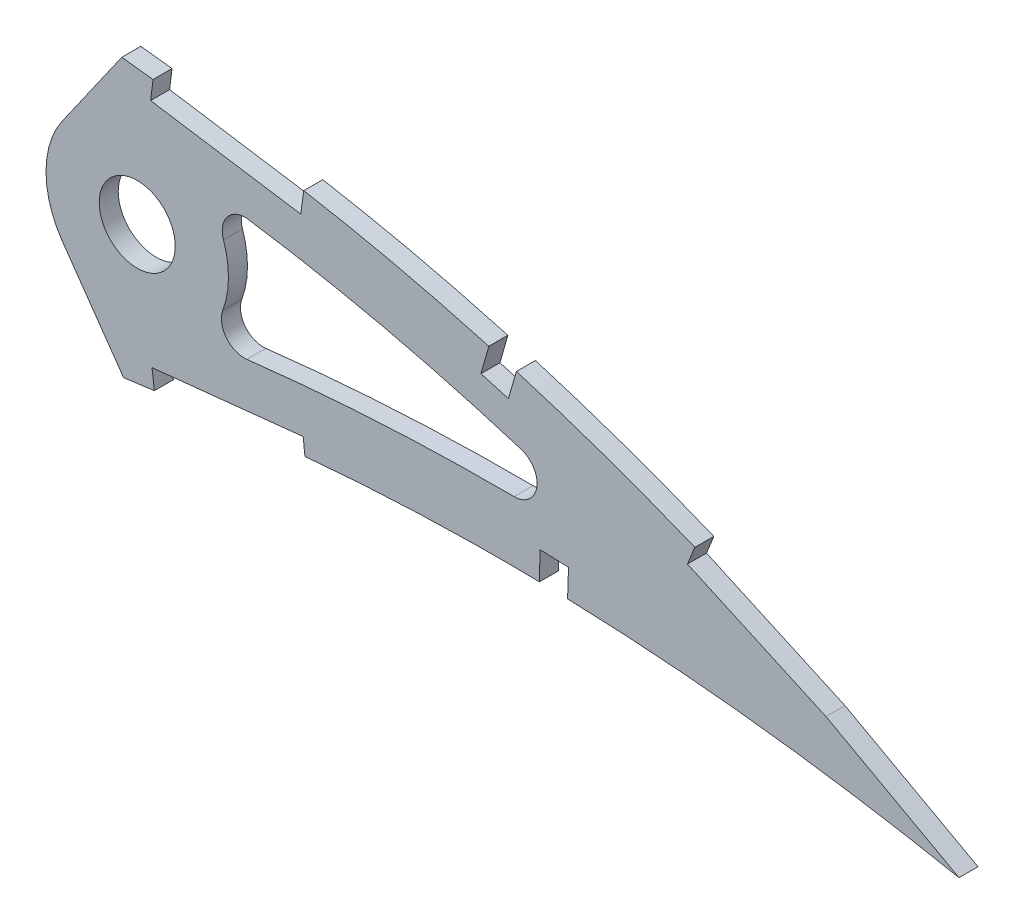
SolidWorks part; units mm, degrees
ref_plane "Front Plane" through (0, 0, 0) normal (0, 0, 1) x (1, 0, 0)
ref_plane "Top Plane" through (0, 0, 0) normal (0, 1, 0) x (1, 0, 0)
ref_plane "Right Plane" through (0, 0, 0) normal (1, 0, 0) x (0, 0, -1)
curve "Curve1"
  spline degree 3 poles (452.1031, 0.7048, 0) (452.0685, 0.7262, 0) (451.9301, 0.8117, 0) (451.6183, 1.003, 0) (451.099, 1.3216, 0) (450.372, 1.7653, 0) (449.438, 2.3329, 0) (448.2963, 3.0204, 0) (446.9478, 3.8257, 0) (445.3928, 4.7448, 0) (443.6314, 5.7736, 0) (441.6643, 6.9077, 0) (439.4916, 8.1409, 0) (437.1143, 9.468, 0) (434.5331, 10.8828, 0) (431.7485, 12.3789, 0) (428.7615, 13.9486, 0) (425.5733, 15.5853, 0) (422.1844, 17.2798, 0) (418.5964, 19.0251, 0) (414.8106, 20.8125, 0) (410.8282, 22.6325, 0) (406.6515, 24.4776, 0) (402.2816, 26.3365, 0) (397.7212, 28.201, 0) (392.972, 30.0605, 0) (388.0369, 31.9065, 0) (382.9178, 33.7272, 0) (377.6186, 35.5144, 0) (372.1418, 37.2567, 0) (366.4913, 38.9446, 0) (360.6704, 40.5671, 0) (354.684, 42.1159, 0) (348.5359, 43.5797, 0) (342.2312, 44.9487, 0) (335.775, 46.2147, 0) (329.1727, 47.3651, 0) (322.4425, 48.3989, 0) (315.6929, 49.2588, 0) (308.9571, 50.1023, 0) (302.2314, 50.8946, 0) (295.4235, 51.6533, 0) (288.5399, 52.3742, 0) (281.5875, 53.055, 0) (274.5733, 53.6928, 0) (267.5046, 54.2857, 0) (260.3883, 54.8303, 0) (253.2318, 55.3259, 0) (246.0422, 55.768, 0) (238.8272, 56.1563, 0) (231.5941, 56.4881, 0) (224.3504, 56.7611, 0) (217.1039, 56.9737, 0) (209.862, 57.1238, 0) (202.6326, 57.2105, 0) (195.4232, 57.2315, 0) (188.2416, 57.1863, 0) (181.0954, 57.0734, 0) (173.9924, 56.8912, 0) (166.9401, 56.6395, 0) (159.9462, 56.3182, 0) (153.0184, 55.9248, 0) (146.164, 55.4618, 0) (139.3909, 54.9271, 0) (132.7063, 54.3206, 0) (126.1174, 53.645, 0) (119.6314, 52.8983, 0) (113.2554, 52.0826, 0) (106.9962, 51.1996, 0) (100.8609, 50.2488, 0) (94.8561, 49.2329, 0) (88.9882, 48.153, 0) (83.2635, 47.0122, 0) (77.6882, 45.8109, 0) (72.2682, 44.5525, 0) (67.0092, 43.2395, 0) (61.9167, 41.874, 0) (56.9959, 40.4594, 0) (52.2519, 38.999, 0) (47.6902, 37.4943, 0) (43.3141, 35.951, 0) (39.1291, 34.3702, 0) (35.1384, 32.7568, 0) (31.3466, 31.113, 0) (27.7567, 29.4439, 0) (24.3726, 27.7512, 0) (21.1967, 26.0397, 0) (18.2324, 24.3122, 0) (15.4823, 22.5717, 0) (12.9477, 20.8227, 0) (10.632, 19.0664, 0) (8.5361, 17.307, 0) (6.6613, 15.5474, 0) (5.0102, 13.7886, 0) (3.5829, 12.0339, 0) (2.3811, 10.2847, 0) (1.4051, 8.5424, 0) (0.6571, 6.8085, 0) (0.1363, 5.084, 0) (-0.1488, 3.3712, 0) (-0.2197, 1.669, 0) (-0.0731, 0.5555, 0) (0, 0, 0) knots 0 0 0 0 0.000254 0.001015 0.002283 0.004057 0.006331 0.009105 0.012374 0.016134 0.02038 0.025106 0.030306 0.035972 0.0421 0.048678 0.055702 0.06316 0.071046 0.07935 0.088063 0.097176 0.106678 0.116562 0.126814 0.137428 0.148394 0.1597 0.171338 0.183298 0.19557 0.208144 0.221012 0.234162 0.247587 0.261277 0.275223 0.289414 0.303771 0.317689 0.331784 0.34604 0.360444 0.374983 0.38964 0.404403 0.419257 0.434187 0.449177 0.464215 0.479284 0.49437 0.509458 0.524532 0.539579 0.554583 0.56953 0.584403 0.599191 0.613877 0.628447 0.642889 0.657186 0.671326 0.685294 0.699078 0.712665 0.726043 0.739198 0.752118 0.764792 0.777208 0.789356 0.801224 0.812804 0.824083 0.835055 0.84571 0.856038 0.866034 0.875689 0.884998 0.893953 0.902553 0.910789 0.918661 0.926166 0.933303 0.940071 0.946475 0.952518 0.958205 0.963547 0.968557 0.97325 0.977651 0.981787 0.985694 0.989415 0.993001 0.996508 1 1 1 1
curve "Curve2"
  spline degree 3 poles (0, 0, 0) (0.1161, -0.5481, 0) (0.3488, -1.6467, 0) (0.9811, -3.2283, 0) (1.8173, -4.7487, 0) (2.8749, -6.2038, 0) (4.147, -7.5932, 0) (5.6306, -8.9184, 0) (7.3243, -10.1787, 0) (9.226, -11.3735, 0) (11.3328, -12.5041, 0) (13.6425, -13.5697, 0) (16.1528, -14.5701, 0) (18.8611, -15.5039, 0) (21.764, -16.3724, 0) (24.8588, -17.1737, 0) (28.1419, -17.9088, 0) (31.6103, -18.5759, 0) (35.26, -19.1755, 0) (39.0874, -19.7075, 0) (43.0885, -20.172, 0) (47.2594, -20.5682, 0) (51.596, -20.8969, 0) (56.0938, -21.1583, 0) (60.7487, -21.3533, 0) (65.556, -21.481, 0) (70.5112, -21.5436, 0) (75.6096, -21.5419, 0) (80.8464, -21.4754, 0) (86.2171, -21.3479, 0) (91.7164, -21.1586, 0) (97.3395, -20.9096, 0) (103.0813, -20.6036, 0) (108.9365, -20.2416, 0) (114.9002, -19.8251, 0) (120.967, -19.3576, 0) (127.1315, -18.8401, 0) (133.3883, -18.2757, 0) (139.7319, -17.6673, 0) (146.1567, -17.0167, 0) (152.6572, -16.327, 0) (159.2275, -15.6004, 0) (165.862, -14.8409, 0) (172.5546, -14.0497, 0) (179.2998, -13.2315, 0) (186.0911, -12.3877, 0) (192.923, -11.5217, 0) (199.7891, -10.6375, 0) (206.6832, -9.7349, 0) (213.5994, -8.8205, 0) (220.5311, -7.8935, 0) (227.4721, -6.9586, 0) (234.4161, -6.0188, 0) (241.3564, -5.0743, 0) (248.2868, -4.1291, 0) (255.2009, -3.1857, 0) (262.0918, -2.2442, 0) (268.9535, -1.3094, 0) (275.779, -0.3811, 0) (282.5619, 0.5389, 0) (289.2958, 1.4477, 0) (295.9744, 2.3443, 0) (302.5907, 3.228, 0) (309.138, 4.0992, 0) (315.5119, 4.9314, 0) (321.6955, 5.769, 0) (327.7099, 6.4556, 0) (333.6493, 7.0417, 0) (339.52, 7.5222, 0) (345.315, 7.9041, 0) (351.0275, 8.19, 0) (356.6509, 8.3839, 0) (362.1779, 8.4917, 0) (367.6017, 8.516, 0) (372.9148, 8.4647, 0) (378.1105, 8.3417, 0) (383.1813, 8.1528, 0) (388.1203, 7.9042, 0) (392.9205, 7.6027, 0) (397.5745, 7.2527, 0) (402.076, 6.8625, 0) (406.4179, 6.4377, 0) (410.5937, 5.9833, 0) (414.5972, 5.5086, 0) (418.4221, 5.0169, 0) (422.0625, 4.5163, 0) (425.5126, 4.0117, 0) (428.7669, 3.5097, 0) (431.8204, 3.015, 0) (434.6681, 2.5342, 0) (437.3055, 2.0718, 0) (439.7281, 1.6323, 0) (441.9324, 1.2212, 0) (443.9143, 0.8406, 0) (445.6709, 0.4968, 0) (447.199, 0.1913, 0) (448.4964, -0.0716, 0) (449.5609, -0.2909, 0) (450.3908, -0.463, 0) (450.9844, -0.5881, 0) (451.3411, -0.6626, 0) (451.4997, -0.6964, 0) (451.5393, -0.7048, 0) knots 0 0 0 0 0.003638 0.007293 0.011028 0.014901 0.018963 0.023258 0.027821 0.032679 0.037853 0.043362 0.049215 0.055422 0.061989 0.068918 0.076211 0.083868 0.091887 0.100266 0.109 0.118085 0.127515 0.137285 0.147388 0.157816 0.168563 0.179619 0.190977 0.202627 0.21456 0.226767 0.239236 0.251959 0.264924 0.27812 0.291536 0.30516 0.318981 0.332985 0.347163 0.361499 0.375981 0.390597 0.405333 0.420175 0.43511 0.450124 0.465203 0.480333 0.495501 0.51069 0.525887 0.541078 0.556247 0.571382 0.586466 0.601485 0.616424 0.631269 0.646007 0.660621 0.675098 0.689423 0.703582 0.716908 0.730009 0.742952 0.755726 0.76832 0.780724 0.792927 0.804916 0.816679 0.828204 0.839475 0.850481 0.861208 0.871639 0.881763 0.891564 0.901027 0.910139 0.918884 0.927249 0.935221 0.942785 0.949928 0.956638 0.962904 0.968712 0.974054 0.978918 0.983297 0.98718 0.990561 0.993433 0.995791 0.99763 0.998946 0.999737 1 1 1 1
sketch "Sketch1" plane through (0, 0, 0) normal (0, 0, 1) x (1, 0, 0)
  line L24 (435.3301, 0.6787) -> (439.1729, -1.6142)
  line L25 (434.7872, -0.6787) -> (439.1729, -1.6142)
  spline S4 degree 3 poles (0, 0) (0.1118, -0.5277) (0.3359, -1.5856) (0.9447, -3.1085) (1.7499, -4.5725) (2.7683, -5.9736) (3.9931, -7.3115) (5.4217, -8.5876) (7.0526, -9.8011) (8.8837, -10.9516) (10.9124, -12.0402) (13.1363, -13.0663) (15.5535, -14.0296) (18.1613, -14.9287) (20.9565, -15.765) (23.9365, -16.5366) (27.0978, -17.2444) (30.4375, -17.8867) (33.9519, -18.4641) (37.6373, -18.9763) (41.49, -19.4236) (45.5061, -19.8051) (49.6818, -20.1216) (54.0128, -20.3734) (58.4949, -20.5611) (63.1239, -20.6841) (67.8952, -20.7443) (72.8045, -20.7427) (77.847, -20.6787) (83.0184, -20.5559) (88.3137, -20.3736) (93.7282, -20.1339) (99.2569, -19.8392) (104.895, -19.4906) (110.6374, -19.0896) (116.4791, -18.6394) (122.4149, -18.1411) (128.4396, -17.5977) (134.5478, -17.0118) (140.7343, -16.3853) (146.9936, -15.7212) (153.3201, -15.0216) (159.7085, -14.2903) (166.1528, -13.5285) (172.6478, -12.7406) (179.1872, -11.9281) (185.7655, -11.0942) (192.377, -10.2428) (199.0153, -9.3738) (205.6749, -8.4933) (212.3494, -7.6007) (219.0329, -6.7005) (225.7193, -5.7955) (232.4021, -4.886) (239.0753, -3.9759) (245.7329, -3.0675) (252.3682, -2.161) (258.9753, -1.2608) (265.5476, -0.3669) (272.0789, 0.5189) (278.563, 1.394) (284.9937, 2.2573) (291.3645, 3.1082) (297.669, 3.9471) (303.8064, 4.7484) (309.7606, 5.555) (315.5518, 6.2161) (321.2709, 6.7805) (326.9238, 7.2431) (332.5038, 7.6108) (338.0044, 7.8861) (343.4191, 8.0729) (348.7411, 8.1767) (353.9637, 8.2001) (359.0797, 8.1506) (364.0826, 8.0323) (368.9653, 7.8503) (373.7211, 7.6109) (378.3431, 7.3206) (382.8245, 6.9836) (387.159, 6.6079) (391.3398, 6.1989) (395.3607, 5.7613) (399.2157, 5.3043) (402.8986, 4.8308) (406.404, 4.3487) (409.7261, 3.8629) (412.8597, 3.3795) (415.7999, 2.9031) (418.5419, 2.4402) (421.0815, 1.9949) (423.4142, 1.5717) (425.5368, 1.1759) (427.445, 0.8095) (429.1365, 0.4784) (430.6079, 0.1842) (431.8572, -0.0689) (432.8822, -0.2801) (433.6813, -0.4458) (434.2529, -0.5663) (434.5964, -0.638) (434.749, -0.6706) (434.7872, -0.6787) knots 0 0 0 0 0.003638 0.007293 0.011028 0.014901 0.018963 0.023258 0.027821 0.032679 0.037853 0.043362 0.049215 0.055422 0.061989 0.068918 0.076211 0.083868 0.091887 0.100266 0.109 0.118085 0.127515 0.137285 0.147388 0.157816 0.168563 0.179619 0.190977 0.202627 0.21456 0.226767 0.239236 0.251959 0.264924 0.27812 0.291536 0.30516 0.318981 0.332985 0.347163 0.361499 0.375981 0.390597 0.405333 0.420175 0.43511 0.450124 0.465203 0.480333 0.495501 0.51069 0.525887 0.541078 0.556247 0.571382 0.586466 0.601485 0.616424 0.631269 0.646007 0.660621 0.675098 0.689423 0.703582 0.716908 0.730009 0.742952 0.755726 0.76832 0.780724 0.792927 0.804916 0.816679 0.828204 0.839475 0.850481 0.861208 0.871639 0.881763 0.891564 0.901027 0.910139 0.918884 0.927249 0.935221 0.942785 0.949928 0.956638 0.962904 0.968712 0.974054 0.978918 0.983297 0.98718 0.990561 0.993433 0.995791 0.99763 0.998946 0.999737 1 1 1 1
  spline S5 degree 3 poles (435.3301, 0.6787) (435.2968, 0.6993) (435.1635, 0.7816) (434.8632, 0.9658) (434.3632, 1.2726) (433.6632, 1.6998) (432.7638, 2.2463) (431.6645, 2.9084) (430.3661, 3.6837) (428.8687, 4.5688) (427.1727, 5.5594) (425.2785, 6.6514) (423.1865, 7.8389) (420.8974, 9.1168) (418.4119, 10.4791) (415.7306, 11.9197) (412.8545, 13.4311) (409.7845, 15.0071) (406.5213, 16.6387) (403.0665, 18.3192) (399.4211, 20.0403) (395.5865, 21.7928) (391.5647, 23.5695) (387.357, 25.3594) (382.9657, 27.1547) (378.3927, 28.9452) (373.6407, 30.7228) (368.7116, 32.4759) (363.609, 34.1968) (358.3353, 35.8745) (352.8945, 37.4998) (347.2896, 39.0621) (341.5252, 40.5534) (335.6052, 41.9629) (329.5344, 43.2811) (323.3177, 44.5002) (316.9603, 45.6079) (310.4799, 46.6033) (303.9807, 47.4313) (297.4948, 48.2435) (291.0186, 49.0064) (284.4633, 49.737) (277.8351, 50.4311) (271.1406, 51.0867) (264.3866, 51.7008) (257.5802, 52.2717) (250.7279, 52.7961) (243.8369, 53.2733) (236.914, 53.699) (229.9667, 54.0729) (223.0019, 54.3924) (216.027, 54.6553) (209.0493, 54.86) (202.0761, 55.0045) (195.1149, 55.088) (188.173, 55.1082) (181.2578, 55.0647) (174.3767, 54.956) (167.5373, 54.7806) (160.7467, 54.5381) (154.0122, 54.2288) (147.3414, 53.85) (140.7414, 53.4041) (134.2195, 52.8893) (127.7829, 52.3053) (121.4385, 51.6548) (115.1931, 50.9357) (109.0536, 50.1503) (103.0266, 49.3001) (97.119, 48.3846) (91.3369, 47.4064) (85.6868, 46.3665) (80.1745, 45.2681) (74.806, 44.1113) (69.5871, 42.8996) (64.5231, 41.6353) (59.6196, 40.3205) (54.8814, 38.9584) (50.3134, 37.5521) (45.9209, 36.1032) (41.7071, 34.6172) (37.6774, 33.0951) (33.8348, 31.5415) (30.1837, 29.9587) (26.7269, 28.3515) (23.4684, 26.7216) (20.4104, 25.0737) (17.5559, 23.4102) (14.9079, 21.7343) (12.4673, 20.0502) (10.2376, 18.359) (8.2194, 16.6649) (6.4142, 14.9706) (4.8244, 13.2771) (3.45, 11.5875) (2.2928, 9.9031) (1.353, 8.2255) (0.6327, 6.5559) (0.1312, 4.8953) (-0.1433, 3.2462) (-0.2116, 1.607) (-0.0704, 0.5349) (0, 0) knots 0 0 0 0 0.000254 0.001015 0.002283 0.004057 0.006331 0.009105 0.012374 0.016134 0.02038 0.025106 0.030306 0.035972 0.0421 0.048678 0.055702 0.06316 0.071046 0.07935 0.088063 0.097176 0.106678 0.116562 0.126814 0.137428 0.148394 0.1597 0.171338 0.183298 0.19557 0.208144 0.221012 0.234162 0.247587 0.261277 0.275223 0.289414 0.303771 0.317689 0.331784 0.34604 0.360444 0.374983 0.38964 0.404403 0.419257 0.434187 0.449177 0.464215 0.479284 0.49437 0.509458 0.524532 0.539579 0.554583 0.56953 0.584403 0.599191 0.613877 0.628447 0.642889 0.657186 0.671326 0.685294 0.699078 0.712665 0.726043 0.739198 0.752118 0.764792 0.777208 0.789356 0.801224 0.812804 0.824083 0.835055 0.84571 0.856038 0.866034 0.875689 0.884998 0.893953 0.902553 0.910789 0.918661 0.926166 0.933303 0.940071 0.946475 0.952518 0.958205 0.963547 0.968557 0.97325 0.977651 0.981787 0.985694 0.989415 0.993001 0.996508 1 1 1 1
extrude "Boss-Extrude1" add sketch "Sketch1" along normal blind 3.175
sketch "Sketch3" plane through (0, 0, 0) normal (0, 0, -1) x (-1, 0, 0)
  circle A1 centre (-292.3838, 26.2554) radius 6.35
extrude "Cut-Extrude2" cut sketch "Sketch3" against normal blind 7.62
sketch "Sketch4" plane through (0, 0, 3.175) normal (0, 0, 1) x (1, 0, 0)
  line L0 (279.8999, 34.9967) -> (289.8019, 49.1382)
  line L1 (279.8999, 17.5141) -> (290.105, 2.9397)
  line L2 (292.3838, 26.2554) -> (322.3057, 26.2554)
  circle A0 centre (292.3838, 26.2554) radius 6.35 construction
  circle A1 centre (292.3838, 26.2554) radius 6.35
  circle A2 centre (292.3838, 26.2554) radius 15.24
  spline S0 degree 3 poles (-1938.1568, -491.7767) (47.0927, 52.1326) (-6.7204, 16.0645) (0.9447, -3.1085) (1.7499, -4.5725) (2.7683, -5.9736) (3.9931, -7.3115) (5.4217, -8.5876) (7.0526, -9.8011) (8.8837, -10.9516) (10.9124, -12.0402) (13.1363, -13.0663) (15.5535, -14.0296) (18.1613, -14.9287) (20.9565, -15.765) (23.9365, -16.5366) (27.0978, -17.2444) (30.4375, -17.8867) (33.9519, -18.4641) (37.6373, -18.9763) (41.49, -19.4236) (45.5061, -19.8051) (49.6818, -20.1216) (54.0128, -20.3734) (58.4949, -20.5611) (63.1239, -20.6841) (67.8952, -20.7443) (72.8045, -20.7427) (77.847, -20.6787) (83.0184, -20.5559) (88.3137, -20.3736) (93.7282, -20.1339) (99.2569, -19.8392) (104.895, -19.4906) (110.6374, -19.0896) (116.4791, -18.6394) (122.4149, -18.1411) (128.4396, -17.5977) (134.5478, -17.0118) (140.7343, -16.3853) (146.9936, -15.7212) (153.3201, -15.0216) (159.7085, -14.2903) (166.1528, -13.5285) (172.6478, -12.7406) (179.1872, -11.9281) (185.7655, -11.0942) (192.377, -10.2428) (199.0153, -9.3738) (205.6749, -8.4933) (212.3494, -7.6007) (219.0329, -6.7005) (225.7193, -5.7955) (232.4021, -4.886) (239.0753, -3.9759) (245.7329, -3.0675) (252.3682, -2.161) (258.9753, -1.2608) (265.5476, -0.3669) (272.0789, 0.5189) (278.563, 1.394) (284.9937, 2.2573) (291.3645, 3.1082) (297.669, 3.9471) (303.8064, 4.7484) (309.7606, 5.555) (315.5518, 6.2161) (321.2709, 6.7805) (326.9238, 7.2431) (332.5038, 7.6108) (338.0044, 7.8861) (343.4191, 8.0729) (348.7411, 8.1767) (353.9637, 8.2001) (359.0797, 8.1506) (364.0826, 8.0323) (368.9653, 7.8503) (373.7211, 7.6109) (378.3431, 7.3206) (382.8245, 6.9836) (387.159, 6.6079) (391.3398, 6.1989) (395.3607, 5.7613) (399.2157, 5.3043) (402.8986, 4.8308) (406.404, 4.3487) (409.7261, 3.8629) (412.8597, 3.3795) (415.7999, 2.9031) (418.5419, 2.4402) (421.0815, 1.9949) (423.4142, 1.5717) (425.5368, 1.1759) (427.445, 0.8095) (429.1365, 0.4784) (430.6079, 0.1842) (431.8572, -0.0689) (432.8822, -0.2801) (433.6813, -0.4458) (434.2529, -0.5663) (448.3411, -3.5068) (461.0644, -11.9601) (889.5705, 1946.1435) knots -0.127812 -0.127812 -0.127812 -0.127812 0.003638 0.007293 0.011028 0.014901 0.018963 0.023258 0.027821 0.032679 0.037853 0.043362 0.049215 0.055422 0.061989 0.068918 0.076211 0.083868 0.091887 0.100266 0.109 0.118085 0.127515 0.137285 0.147388 0.157816 0.168563 0.179619 0.190977 0.202627 0.21456 0.226767 0.239236 0.251959 0.264924 0.27812 0.291536 0.30516 0.318981 0.332985 0.347163 0.361499 0.375981 0.390597 0.405333 0.420175 0.43511 0.450124 0.465203 0.480333 0.495501 0.51069 0.525887 0.541078 0.556247 0.571382 0.586466 0.601485 0.616424 0.631269 0.646007 0.660621 0.675098 0.689423 0.703582 0.716908 0.730009 0.742952 0.755726 0.76832 0.780724 0.792927 0.804916 0.816679 0.828204 0.839475 0.850481 0.861208 0.871639 0.881763 0.891564 0.901027 0.910139 0.918884 0.927249 0.935221 0.942785 0.949928 0.956638 0.962904 0.968712 0.974054 0.978918 0.983297 0.98718 0.990561 0.993433 0.995791 0.99763 0.998946 0.999737 1.094845 1.094845 1.094845 1.094845 only from (0, 0) to (434.7872, -0.6787) construction
  spline S1 degree 3 poles (1523.9168, 1677.8723) (459.4041, -20.0575) (448.5517, -7.4305) (434.8632, 0.9658) (434.3632, 1.2726) (433.6632, 1.6998) (432.7638, 2.2463) (431.6645, 2.9084) (430.3661, 3.6837) (428.8687, 4.5688) (427.1727, 5.5594) (425.2785, 6.6514) (423.1865, 7.8389) (420.8974, 9.1168) (418.4119, 10.4791) (415.7306, 11.9197) (412.8545, 13.4311) (409.7845, 15.0071) (406.5213, 16.6387) (403.0665, 18.3192) (399.4211, 20.0403) (395.5865, 21.7928) (391.5647, 23.5695) (387.357, 25.3594) (382.9657, 27.1547) (378.3927, 28.9452) (373.6407, 30.7228) (368.7116, 32.4759) (363.609, 34.1968) (358.3353, 35.8745) (352.8945, 37.4998) (347.2896, 39.0621) (341.5252, 40.5534) (335.6052, 41.9629) (329.5344, 43.2811) (323.3177, 44.5002) (316.9603, 45.6079) (310.4799, 46.6033) (303.9807, 47.4313) (297.4948, 48.2435) (291.0186, 49.0064) (284.4633, 49.737) (277.8351, 50.4311) (271.1406, 51.0867) (264.3866, 51.7008) (257.5802, 52.2717) (250.7279, 52.7961) (243.8369, 53.2733) (236.914, 53.699) (229.9667, 54.0729) (223.0019, 54.3924) (216.027, 54.6553) (209.0493, 54.86) (202.0761, 55.0045) (195.1149, 55.088) (188.173, 55.1082) (181.2578, 55.0647) (174.3767, 54.956) (167.5373, 54.7806) (160.7467, 54.5381) (154.0122, 54.2288) (147.3414, 53.85) (140.7414, 53.4041) (134.2195, 52.8893) (127.7829, 52.3053) (121.4385, 51.6548) (115.1931, 50.9357) (109.0536, 50.1503) (103.0266, 49.3001) (97.119, 48.3846) (91.3369, 47.4064) (85.6868, 46.3665) (80.1745, 45.2681) (74.806, 44.1113) (69.5871, 42.8996) (64.5231, 41.6353) (59.6196, 40.3205) (54.8814, 38.9584) (50.3134, 37.5521) (45.9209, 36.1032) (41.7071, 34.6172) (37.6774, 33.0951) (33.8348, 31.5415) (30.1837, 29.9587) (26.7269, 28.3515) (23.4684, 26.7216) (20.4104, 25.0737) (17.5559, 23.4102) (14.9079, 21.7343) (12.4673, 20.0502) (10.2376, 18.359) (8.2194, 16.6649) (6.4142, 14.9706) (4.8244, 13.2771) (3.45, 11.5875) (2.2928, 9.9031) (1.353, 8.2255) (0.6327, 6.5559) (0.1312, 4.8953) (-0.1433, 3.2462) (-1.0017, -17.3492) (61.8716, -33.4146) (-1991.1542, -180.949) knots -0.101807 -0.101807 -0.101807 -0.101807 0.000254 0.001015 0.002283 0.004057 0.006331 0.009105 0.012374 0.016134 0.02038 0.025106 0.030306 0.035972 0.0421 0.048678 0.055702 0.06316 0.071046 0.07935 0.088063 0.097176 0.106678 0.116562 0.126814 0.137428 0.148394 0.1597 0.171338 0.183298 0.19557 0.208144 0.221012 0.234162 0.247587 0.261277 0.275223 0.289414 0.303771 0.317689 0.331784 0.34604 0.360444 0.374983 0.38964 0.404403 0.419257 0.434187 0.449177 0.464215 0.479284 0.49437 0.509458 0.524532 0.539579 0.554583 0.56953 0.584403 0.599191 0.613877 0.628447 0.642889 0.657186 0.671326 0.685294 0.699078 0.712665 0.726043 0.739198 0.752118 0.764792 0.777208 0.789356 0.801224 0.812804 0.824083 0.835055 0.84571 0.856038 0.866034 0.875689 0.884998 0.893953 0.902553 0.910789 0.918661 0.926166 0.933303 0.940071 0.946475 0.952518 0.958205 0.963547 0.968557 0.97325 0.977651 0.981787 0.985694 0.989415 0.993001 0.996508 1.122415 1.122415 1.122415 1.122415 only from (435.3301, 0.6787) to (0, 0) construction
  spline S2 degree 3 poles (187.1339, -10.9169) (188.8786, -10.6932) (192.8369, -10.1826) (199.0153, -9.3738) (205.6749, -8.4933) (212.3494, -7.6007) (219.0329, -6.7005) (225.7193, -5.7955) (232.4021, -4.886) (239.0753, -3.9759) (245.7329, -3.0675) (252.3682, -2.161) (258.9753, -1.2608) (265.5476, -0.3669) (272.0789, 0.5189) (278.563, 1.394) (284.9937, 2.2573) (291.3645, 3.1082) (297.669, 3.9471) (303.8064, 4.7484) (309.7606, 5.555) (315.5518, 6.2161) (321.2709, 6.7805) (326.9238, 7.2431) (332.5038, 7.6108) (338.0044, 7.8861) (343.4191, 8.0729) (348.7411, 8.1767) (353.9637, 8.2001) (359.0797, 8.1506) (364.0826, 8.0323) (368.9653, 7.8503) (373.7211, 7.6109) (378.3431, 7.3206) (382.8245, 6.9836) (387.159, 6.6079) (391.3398, 6.1989) (395.3607, 5.7613) (399.2157, 5.3043) (402.8986, 4.8308) (406.404, 4.3487) (409.7261, 3.8629) (412.8597, 3.3795) (415.7999, 2.9031) (418.5419, 2.4402) (421.0815, 1.9949) (423.4142, 1.5717) (425.5368, 1.1759) (427.445, 0.8095) (429.1365, 0.4784) (430.6079, 0.1842) (431.8572, -0.0689) (432.8822, -0.2801) (433.6813, -0.4458) (434.2529, -0.5663) (434.5964, -0.638) (434.749, -0.6706) (434.7872, -0.6787) knots 0.438243 0.438243 0.438243 0.438243 0.450124 0.465203 0.480333 0.495501 0.51069 0.525887 0.541078 0.556247 0.571382 0.586466 0.601485 0.616424 0.631269 0.646007 0.660621 0.675098 0.689423 0.703582 0.716908 0.730009 0.742952 0.755726 0.76832 0.780724 0.792927 0.804916 0.816679 0.828204 0.839475 0.850481 0.861208 0.871639 0.881763 0.891564 0.901027 0.910139 0.918884 0.927249 0.935221 0.942785 0.949928 0.956638 0.962904 0.968712 0.974054 0.978918 0.983297 0.98718 0.990561 0.993433 0.995791 0.99763 0.998946 0.999737 1 1 1 1
  spline S3 degree 3 poles (435.3301, 0.6787) (435.2968, 0.6993) (435.1635, 0.7816) (434.8632, 0.9658) (434.3632, 1.2726) (433.6632, 1.6998) (432.7638, 2.2463) (431.6645, 2.9084) (430.3661, 3.6837) (428.8687, 4.5688) (427.1727, 5.5594) (425.2785, 6.6514) (423.1865, 7.8389) (420.8974, 9.1168) (418.4119, 10.4791) (415.7306, 11.9197) (412.8545, 13.4311) (409.7845, 15.0071) (406.5213, 16.6387) (403.0665, 18.3192) (399.4211, 20.0403) (395.5865, 21.7928) (391.5647, 23.5695) (387.357, 25.3594) (382.9657, 27.1547) (378.3927, 28.9452) (373.6407, 30.7228) (368.7116, 32.4759) (363.609, 34.1968) (358.3353, 35.8745) (352.8945, 37.4998) (347.2896, 39.0621) (341.5252, 40.5534) (335.6052, 41.9629) (329.5344, 43.2811) (323.3177, 44.5002) (316.9603, 45.6079) (310.4799, 46.6033) (303.9807, 47.4313) (297.4948, 48.2435) (291.0186, 49.0064) (284.4633, 49.737) (277.8351, 50.4311) (271.1406, 51.0867) (264.3866, 51.7008) (257.5802, 52.2717) (250.7279, 52.7961) (243.8369, 53.2733) (236.914, 53.699) (229.9667, 54.0729) (223.0019, 54.3924) (216.027, 54.6553) (209.0493, 54.86) (202.0761, 55.0045) (195.1149, 55.088) (188.173, 55.1082) (181.2578, 55.0647) (174.2351, 54.9537) (169.519, 54.8313) (167.0972, 54.7555) knots 0 0 0 0 0.000254 0.001015 0.002283 0.004057 0.006331 0.009105 0.012374 0.016134 0.02038 0.025106 0.030306 0.035972 0.0421 0.048678 0.055702 0.06316 0.071046 0.07935 0.088063 0.097176 0.106678 0.116562 0.126814 0.137428 0.148394 0.1597 0.171338 0.183298 0.19557 0.208144 0.221012 0.234162 0.247587 0.261277 0.275223 0.289414 0.303771 0.317689 0.331784 0.34604 0.360444 0.374983 0.38964 0.404403 0.419257 0.434187 0.449177 0.464215 0.479284 0.49437 0.509458 0.524532 0.539579 0.554583 0.56953 0.584403 0.600109 0.600109 0.600109 0.600109
  spline S4 degree 1 poles (429.9904, -7.965) (167.4152, 44.6005) knots 0 0 1 1 construction
  spline S5 degree 3 poles (429.9904, -7.965) (429.8456, -7.8755) (429.5612, -7.701) (428.9465, -7.324) (427.9014, -6.6866) (425.7991, -5.417) (421.56, -2.9105) (413.0081, 1.9392) (395.5546, 10.9948) (374.8817, 19.775) (353.6107, 26.8378) (337.3911, 31.2471) (323.7235, 34.1538) (314.0324, 35.7912) (308.5417, 36.5984) (304.3526, 37.1433) (300.0459, 37.6853) (294.369, 38.387) (284.4102, 39.5433) (270.1677, 41.0169) (253.0537, 42.4791) (230.2149, 44.0078) (201.6364, 45.0891) (178.8209, 44.9576) (167.4152, 44.6005) knots 0 0 0 0 0.001172 0.002344 0.004688 0.009377 0.018753 0.037507 0.075014 0.150027 0.187534 0.225041 0.262548 0.281301 0.290678 0.300055 0.309431 0.318808 0.337561 0.375068 0.412575 0.450082 0.525095 0.600109 0.600109 0.600109 0.600109
  spline S6 degree 1 poles (185.842, -0.8394) (436.9067, 9.2578) knots 0 0 1 1 construction
  spline S7 degree 3 poles (185.842, -0.8394) (196.1308, 0.4796) (216.6819, 3.2169) (242.4257, 6.737) (263.0318, 9.5469) (278.5062, 11.6407) (290.0912, 13.192) (297.8571, 14.2176) (301.7093, 14.7217) (305.5466, 15.2385) (309.5506, 15.7549) (313.5473, 16.2111) (318.8532, 16.7615) (328.1897, 17.5737) (341.5363, 18.2864) (357.5775, 18.4367) (378.9369, 17.7156) (400.1983, 15.6548) (418.6043, 12.7905) (427.7773, 11.1037) (432.324, 10.2055) (434.4543, 9.7697) (435.418, 9.5702) (435.9281, 9.4638) (436.3812, 9.3684) (436.736, 9.2942) (436.9067, 9.2578) knots 0.438243 0.438243 0.438243 0.438243 0.508463 0.578682 0.613792 0.648902 0.684012 0.692789 0.701567 0.710344 0.719122 0.727899 0.736676 0.754231 0.789341 0.824451 0.859561 0.92978 0.96489 0.982445 0.991223 0.995611 0.996708 0.997806 0.998903 1 1 1 1
  dimension "D1" = 30.48
  dimension "D2" = 55
  dimension "D3" = 55
  dimension "D4" = 10.16
extrude "Cut-Extrude3" cut sketch "Sketch4" against normal through all
sketch "Sketch5" plane through (0, 0, 3.175) normal (0, 0, 1) x (1, 0, 0)
  line L0 (320.1272, 44.5418) -> (295.01, 48.427)
  line L1 (320.1272, 44.5418) -> (295.01, 48.427)
  line L2 (295.01, 48.427) -> (294.6173, 45.2769)
  line L3 (295.01, 48.427) -> (294.6173, 45.2769)
  line L4 (320.1059, 9.4131) -> (294.8543, 6.7636)
  line L5 (320.1059, 9.4131) -> (294.8543, 6.7636)
  line L6 (294.8543, 6.7636) -> (295.2516, 3.6136)
  line L7 (294.8543, 6.7636) -> (295.2516, 3.6136)
  line L8 (355.7068, 36.5934) -> (351.1052, 37.9406)
  line L9 (355.7068, 36.5934) -> (351.1052, 37.9406)
  line L10 (351.1052, 37.9406) -> (349.802, 33.3604)
  line L11 (351.1052, 37.9406) -> (349.802, 33.3604)
  line L12 (364.4262, 12.6759) -> (359.6672, 12.8341)
  line L13 (364.4262, 12.6759) -> (359.6672, 12.8341)
  line L14 (359.6672, 12.8341) -> (359.5707, 8.0733)
  line L15 (359.6672, 12.8341) -> (359.5707, 8.0733)
  line L16 (408.6237, 15.5192) -> (385.4959, 26.0108)
  line L17 (408.6237, 15.5192) -> (385.4959, 26.0108)
  line L18 (385.4959, 26.0108) -> (384.299, 23.0709)
  line L19 (385.4959, 26.0108) -> (384.299, 23.0709)
  line L20 (431.219, 3.1381) -> (408.9549, 15.3623)
  line L21 (431.219, 3.1381) -> (408.9549, 15.3623)
  line L22 (429.691, 0.3551) -> (431.219, 3.1381)
  line L23 (429.691, 0.3551) -> (431.219, 3.1381)
  line L24 (407.4269, 12.5793) -> (429.691, 0.3551)
  line L25 (407.4269, 12.5793) -> (429.691, 0.3551)
  line L26 (384.299, 23.0709) -> (407.4269, 12.5793)
  line L27 (384.299, 23.0709) -> (407.4269, 12.5793)
  line L28 (354.3821, 32.0572) -> (355.7068, 36.5934)
  line L29 (354.3821, 32.0572) -> (355.7068, 36.5934)
  line L30 (349.802, 33.3604) -> (354.3821, 32.0572)
  line L31 (349.802, 33.3604) -> (354.3821, 32.0572)
  line L32 (364.2691, 7.9477) -> (364.4262, 12.6759)
  line L33 (364.2691, 7.9477) -> (364.4262, 12.6759)
  line L34 (359.5707, 8.0733) -> (364.2691, 7.9477)
  line L35 (359.5707, 8.0733) -> (364.2691, 7.9477)
  line L36 (319.7015, 41.3956) -> (320.1272, 44.5418)
  line L37 (319.7015, 41.3956) -> (320.1272, 44.5418)
  line L38 (294.6173, 45.2769) -> (319.7015, 41.3956)
  line L39 (294.6173, 45.2769) -> (319.7015, 41.3956)
  line L40 (295.2516, 3.6136) -> (320.438, 6.2568)
  line L41 (295.2516, 3.6136) -> (320.438, 6.2568)
  line L42 (320.438, 6.2568) -> (320.1059, 9.4131)
  line L43 (320.438, 6.2568) -> (320.1059, 9.4131)
  line L44 (295.01, 48.427) -> (295.2636, 50.461)
  line L45 (320.1272, 44.5418) -> (320.7205, 48.9265)
  line L46 (351.1052, 37.9406) -> (351.4797, 39.2198)
  line L47 (355.7068, 36.5934) -> (356.1012, 37.9406)
  line L48 (385.4959, 26.0108) -> (388.4224, 33.1994)
  line L49 (388.4224, 33.1994) -> (461.874, 33.1994)
  line L50 (461.874, 33.1994) -> (461.874, -17.3152)
  line L51 (461.874, -17.3152) -> (429.691, 0.3551)
  line L52 (359.5707, 8.0733) -> (359.5097, 5.7935)
  line L53 (364.2691, 7.9477) -> (364.1797, 4.6031)
  line L54 (295.2516, 3.6136) -> (295.6613, 0.3654)
extrude "Cut-Extrude4" cut sketch "Sketch5" against normal through all
fillet "Fillet1" radius 3.81 3 edges at (380.0127, 17.3785, 1.5875) (302.463, 14.8244, 1.5875) (302.852, 37.3313, 1.5875)
